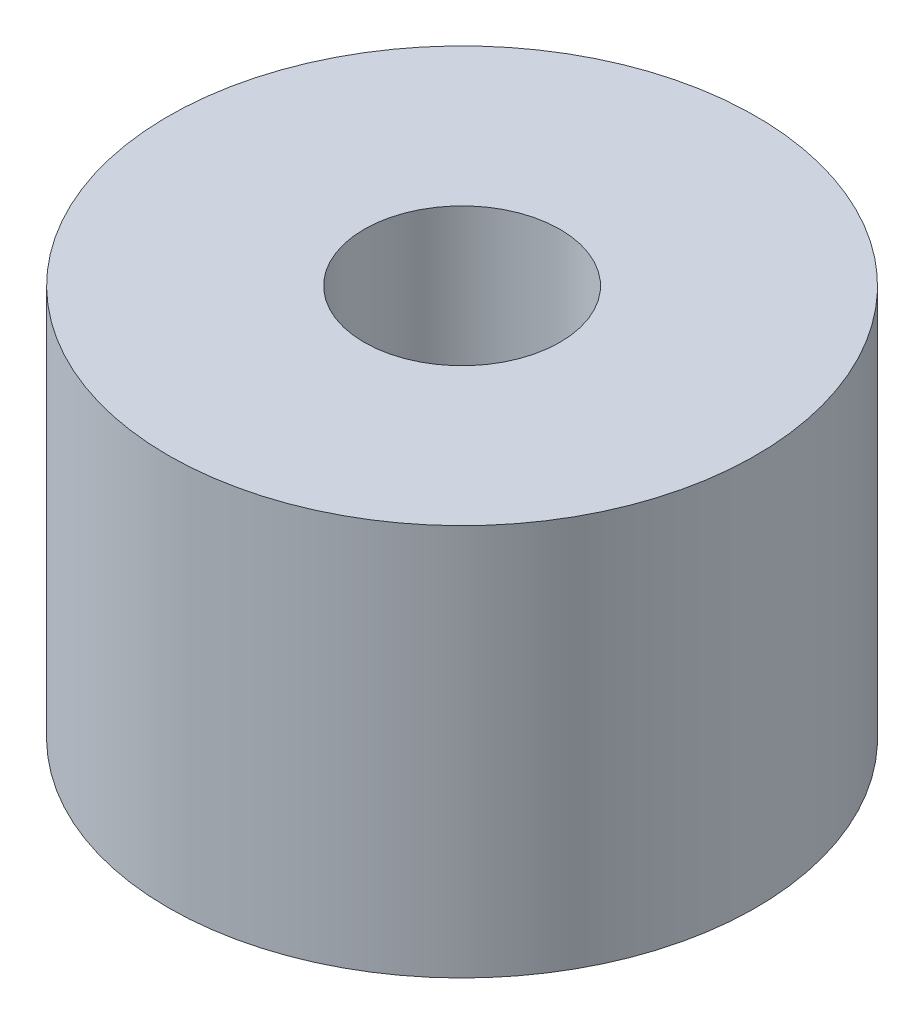
SolidWorks part; units mm, degrees
ref_plane "Face" through (0, 0, 0) normal (0, 0, 1) x (1, 0, 0)
ref_plane "Dessus" through (0, 0, 0) normal (0, 1, 0) x (1, 0, 0)
ref_plane "Droite" through (0, 0, 0) normal (1, 0, 0) x (0, 0, -1)
sketch "Esquisse1" plane through (0, 0, 0) normal (0, 1, 0) x (1, 0, 0)
  circle A0 centre (0, 0) radius 15
  circle A1 centre (0, 0) radius 5
  dimension "D1" = 30
  dimension "D2" = 10
extrude "Extrusion1" add sketch "Esquisse1" along normal blind 20
